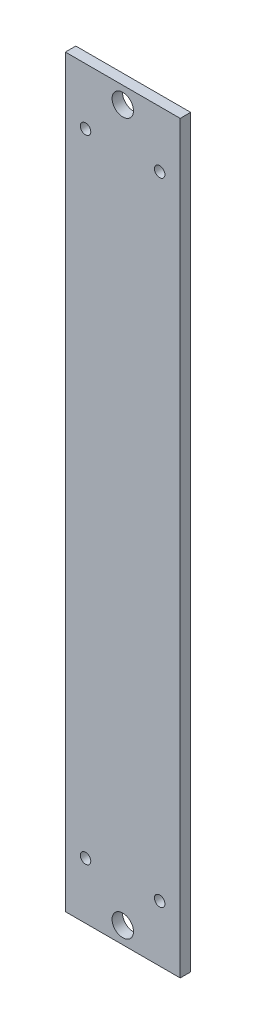
SolidWorks part; units mm, degrees
ref_plane "Front Plane" through (0, 0, 0) normal (0, 0, 1) x (1, 0, 0)
ref_plane "Top Plane" through (0, 0, 0) normal (0, 1, 0) x (1, 0, 0)
ref_plane "Right Plane" through (0, 0, 0) normal (1, 0, 0) x (0, 0, -1)
sketch "Sketch1" plane through (0, 0, 0) normal (0, 0, 1) x (1, 0, 0)
  line L0 (17.05, 216) -> (17.05, 5) construction
  line L1 (0, 0) -> (34.1, 0)
  line L2 (0, 0) -> (0, 221)
  line L3 (0, 221) -> (34.1, 221)
  line L4 (34.1, 0) -> (34.1, 221)
  line L5 (17.05, 216) -> (17.05, 221) construction
  line L6 (17.05, 5) -> (17.05, 0) construction
  line L7 (0, 204.25) -> (34.1, 204.25) construction
  line L8 (9.9209, 221) -> (9.9209, 204.25) construction
  line L9 (0, 16.75) -> (34.1, 16.75) construction
  line L10 (9.6191, 0) -> (9.6191, 16.75) construction
  line L11 (6, 204.25) -> (6, 16.75) construction
  line L12 (28, 16.75) -> (28, 204.25) construction
  circle A0 centre (17.05, 216) radius 3.175
  circle A1 centre (17.05, 5) radius 3.175
  circle A2 centre (6, 204.25) radius 1.55
  circle A3 centre (28, 204.25) radius 1.55
  circle A4 centre (28, 16.75) radius 1.55
  circle A5 centre (6, 16.75) radius 1.55
extrude "Boss-Extrude1" add sketch "Sketch1" along normal blind 3.1
